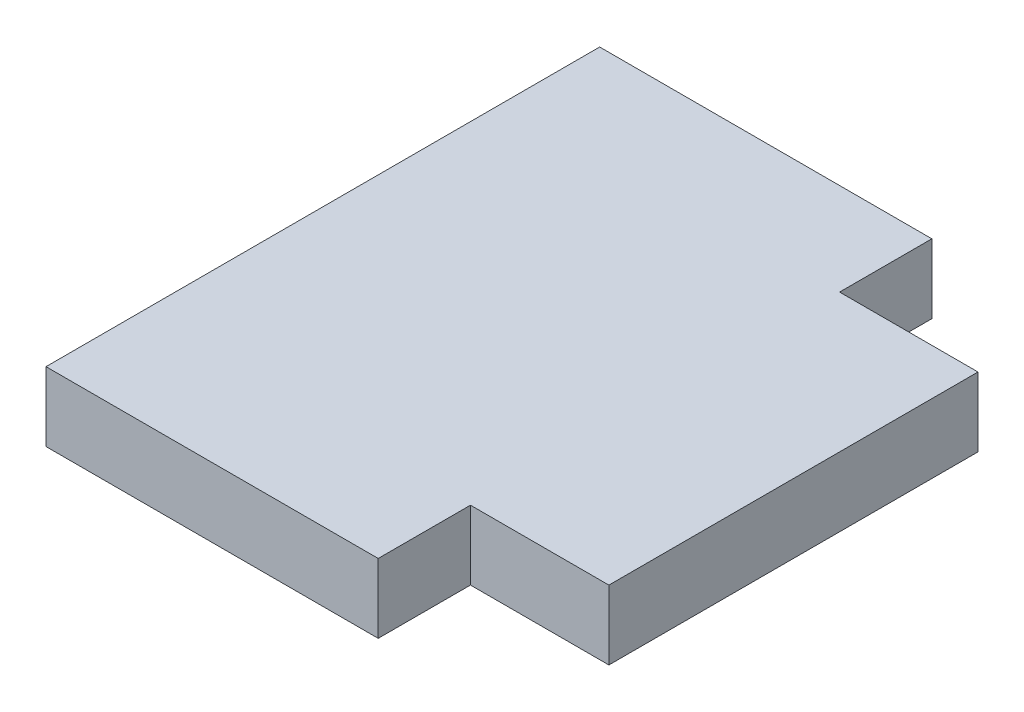
SolidWorks part; units mm, degrees
ref_plane "Спереди" through (0, 0, 0) normal (0, 0, 1) x (1, 0, 0)
ref_plane "Сверху" through (0, 0, 0) normal (0, 1, 0) x (1, 0, 0)
ref_plane "Справа" through (0, 0, 0) normal (1, 0, 0) x (0, 0, -1)
sketch "Эскиз1" plane through (0, 0, 0) normal (0, 1, 0) x (1, 0, 0)
  line L1 (0, 0) -> (10.2, 0)
  line L2 (0, 0) -> (0, 12)
  line L3 (0, 12) -> (10.2, 12)
  line L4 (10.2, 0) -> (10.2, 12)
  dimension "D1" = 10.2
  dimension "D2" = 12
extrude "Бобышка-Вытянуть1" add sketch "Эскиз1" along normal blind 1.5
sketch "Эскиз2" plane through (0, 1.5, 0) normal (0, 1, 0) x (1, 0, 0)
  line L0 (10.2, 6) -> (0, 6) construction
  line L1 (10.2, 0) -> (10.2, 12) construction
  line L2 (0, 12) -> (0, 0) construction
  line L3 (10.2, 12) -> (0, 12) construction
  line L4 (7.2, 12) -> (10.2, 12)
  line L5 (7.2, 12) -> (7.2, 10)
  line L6 (7.2, 10) -> (10.2, 10)
  line L7 (10.2, 12) -> (10.2, 10)
  line L8 (7.2, 2) -> (10.2, 2)
  line L9 (7.2, 0) -> (7.2, 2)
  line L10 (7.2, 0) -> (10.2, 0)
  line L11 (10.2, 0) -> (10.2, 2)
  dimension "D1" = 3
  dimension "D2" = 2
extrude "Вырез-Вытянуть1" cut sketch "Эскиз2" against normal through all
sketch "Эскиз3" plane through (0, 1.5, 0) normal (0, 1, 0) x (1, 0, 0)
  line L8 (0, 0.65) -> (0.45, 0.65)
  line L9 (0.45, 0.65) -> (0.45, 1.2)
  line L10 (0.45, 1.2) -> (1.15, 1.2)
  line L11 (1.15, 1.2) -> (1.15, 0.65)
  line L12 (1.15, 0.65) -> (1.6, 0.65)
  line L13 (1.6, 0.65) -> (1.6, 2.15)
  line L14 (1.6, 2.15) -> (0, 2.15)
  line L15 (0, 2.15) -> (0, 0.65)
  line L16 (0, 0.65) -> (0.45, 0.65)
  line L17 (0.45, 0.65) -> (0.45, 1.2)
  line L18 (0.45, 1.2) -> (1.15, 1.2)
  line L19 (1.15, 1.2) -> (1.15, 0.65)
  line L20 (1.15, 0.65) -> (1.6, 0.65)
  line L21 (1.6, 0.65) -> (1.6, 2.15)
  line L22 (1.6, 2.15) -> (0, 2.15)
  line L23 (0, 2.15) -> (0, 0.65)
  line L24 (5.6, 0.65) -> (6.05, 0.65)
  line L25 (6.05, 0.65) -> (6.05, 1.2)
  line L26 (6.05, 1.2) -> (6.75, 1.2)
  line L27 (6.75, 1.2) -> (6.75, 0.65)
  line L28 (6.75, 0.65) -> (7.2, 0.65)
  line L29 (7.2, 0.65) -> (7.2, 2.15)
  line L30 (7.2, 2.15) -> (5.6, 2.15)
  line L31 (5.6, 2.15) -> (5.6, 0.65)
  line L32 (5.6, 0.65) -> (6.05, 0.65)
  line L33 (6.05, 0.65) -> (6.05, 1.2)
  line L34 (6.05, 1.2) -> (6.75, 1.2)
  line L35 (6.75, 1.2) -> (6.75, 0.65)
  line L36 (6.75, 0.65) -> (7.2, 0.65)
  line L37 (7.2, 0.65) -> (7.2, 2.15)
  line L38 (7.2, 2.15) -> (5.6, 2.15)
  line L39 (5.6, 2.15) -> (5.6, 0.65)
  line L40 (6.75, 10.8) -> (6.05, 10.8)
  line L41 (6.05, 10.8) -> (6.05, 11.35)
  line L42 (6.05, 11.35) -> (5.6, 11.35)
  line L43 (5.6, 11.35) -> (5.6, 9.85)
  line L44 (5.6, 9.85) -> (7.2, 9.85)
  line L45 (7.2, 9.85) -> (7.2, 11.35)
  line L46 (7.2, 11.35) -> (6.75, 11.35)
  line L47 (6.75, 11.35) -> (6.75, 10.8)
  line L48 (6.75, 10.8) -> (6.05, 10.8)
  line L49 (6.05, 10.8) -> (6.05, 11.35)
  line L50 (6.05, 11.35) -> (5.6, 11.35)
  line L51 (5.6, 11.35) -> (5.6, 9.85)
  line L52 (5.6, 9.85) -> (7.2, 9.85)
  line L53 (7.2, 9.85) -> (7.2, 11.35)
  line L54 (7.2, 11.35) -> (6.75, 11.35)
  line L55 (6.75, 11.35) -> (6.75, 10.8)
  line L56 (1.15, 10.8) -> (0.45, 10.8)
  line L57 (0.45, 10.8) -> (0.45, 11.35)
  line L58 (0.45, 11.35) -> (0, 11.35)
  line L59 (0, 11.35) -> (0, 9.85)
  line L60 (0, 9.85) -> (1.6, 9.85)
  line L61 (1.6, 9.85) -> (1.6, 11.35)
  line L62 (1.6, 11.35) -> (1.15, 11.35)
  line L63 (1.15, 11.35) -> (1.15, 10.8)
  line L64 (1.15, 10.8) -> (0.45, 10.8)
  line L65 (0.45, 10.8) -> (0.45, 11.35)
  line L66 (0.45, 11.35) -> (0, 11.35)
  line L67 (0, 11.35) -> (0, 9.85)
  line L68 (0, 9.85) -> (1.6, 9.85)
  line L69 (1.6, 9.85) -> (1.6, 11.35)
  line L70 (1.6, 11.35) -> (1.15, 11.35)
  line L71 (1.15, 11.35) -> (1.15, 10.8)
  line L72 (0, 0) -> (7.2, 0)
  line L73 (7.2, 0) -> (7.2, 2)
  line L74 (7.2, 2) -> (10.2, 2)
  line L75 (10.2, 2) -> (10.2, 10)
  line L76 (10.2, 10) -> (7.2, 10)
  line L77 (7.2, 10) -> (7.2, 12)
  line L78 (7.2, 12) -> (0, 12)
  line L79 (0, 12) -> (0, 0)
  line L80 (0, 0) -> (7.2, 0)
  line L81 (7.2, 0) -> (7.2, 2)
  line L82 (7.2, 2) -> (10.2, 2)
  line L83 (10.2, 2) -> (10.2, 10)
  line L84 (10.2, 10) -> (7.2, 10)
  line L85 (7.2, 10) -> (7.2, 12)
  line L86 (7.2, 12) -> (0, 12)
  line L87 (0, 12) -> (0, 0)
  dimension "D1" = 0
  dimension "D2" = 0
  dimension "D3" = 0
  dimension "D4" = 0
  dimension "D5" = 0
